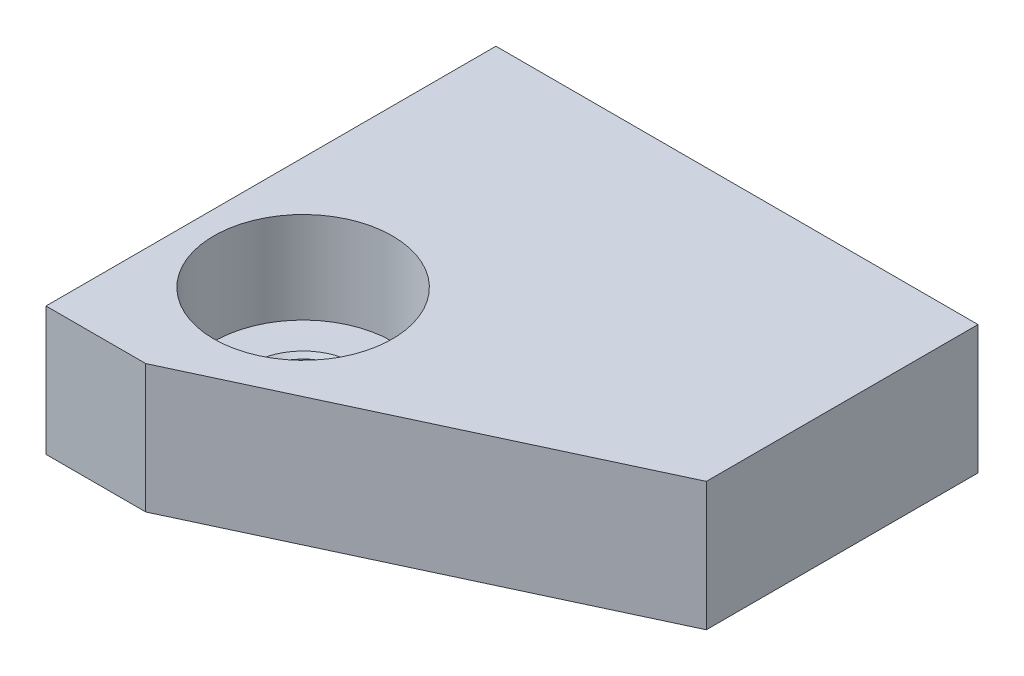
SolidWorks part; units mm, degrees
material "6063-T1"
ref_plane "Спереди" through (0, 0, 0) normal (0, 0, 1) x (1, 0, 0)
ref_plane "Сверху" through (0, 0, 0) normal (0, 1, 0) x (1, 0, 0)
ref_plane "Справа" through (0, 0, 0) normal (1, 0, 0) x (0, 0, -1)
sketch "Эскиз1" plane through (0, 0, 0) normal (0, 1, 0) x (1, 0, 0)
  line L0 (0, 0) -> (0, -14)
  line L1 (3.1037, -14) -> (0, -14)
  line L2 (15, -8.4527) -> (15, 0)
  line L3 (15, 0) -> (0, 0)
  line L4 (3.1037, -14) -> (15, -8.4527)
  dimension "D1" = 15
  dimension "D2" = 14
  dimension "D3" = 25
  dimension "D4" = 14
extrude "Бобышка-Вытянуть1" add sketch "Эскиз1" along normal blind 4
hole_wizard "Цековка для  винта с внутренним шестигранником #41" positions "Эскиз3" profile "Эскиз2" counterbore size "#4" standard "Ansi (в дюймах)" end condition through all
sketch "Эскиз3" plane through (0, 4, 0) normal (0, 1, 0) x (-1, 0, 0)
  line L0 (-15, 0) -> (0, 0) construction
  line L1 (0, 0) -> (0, 14) construction
  point P0 (-3.5, 9.5)
  dimension "D1" = 9.5
  dimension "D2" = 3.5
sketch "Эскиз2" plane through (3.5, 4, 9.5) normal (1, 0, 0) x (0, 0, 1)
  line L0 (0, 0) -> (0, 4)
  line L1 (1.4732, 3.873) -> (1.6002, 4)
  line L2 (1.4732, 3.873) -> (1.4732, 2.9718)
  line L3 (1.4732, 2.9718) -> (1.6002, 2.8448)
  line L4 (1.6002, 2.8448) -> (2.7788, 2.8448)
  line L5 (2.7788, 2.8448) -> (2.7788, 0)
  line L7 (2.7788, 0) -> (0, 0)
  line L9 (-1.4732, 2.9718) -> (-1.6002, 2.8448) construction
  line L11 (0, -6.35) -> (0, 107.95) construction
  line L12 (1.6002, 4) -> (0, 4)
  line L13 (-1.4732, 3.873) -> (-1.6002, 4) construction
  dimension "Диаметр сквозного отверстия" = 2.9464
  dimension "Глубина сквозного отверстия" = 4
  dimension "Диаметр цековки" = 5.5575
  dimension "Глубина цековки" = 2.8448
  dimension "Диаметр средней зенковки" = 3.2004
  dimension "Угол средней зенковки" = 90
  dimension "Диаметр задней зенковки" = 3.2004
  dimension "Угол задней зенковки" = 90
